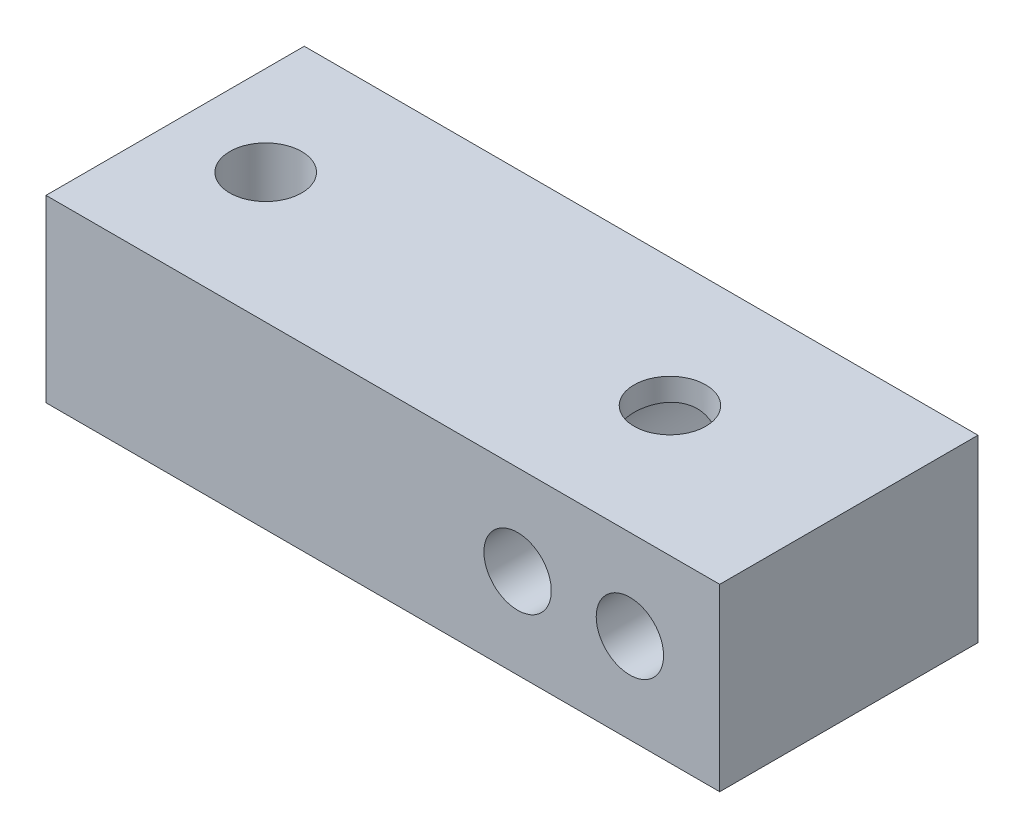
SolidWorks part; units mm, degrees
ref_plane "Front Plane" through (0, 0, 0) normal (0, 0, 1) x (1, 0, 0)
ref_plane "Top Plane" through (0, 0, 0) normal (0, 1, 0) x (1, 0, 0)
ref_plane "Right Plane" through (0, 0, 0) normal (1, 0, 0) x (0, 0, -1)
sketch "Sketch1" plane through (0, 0, 0) normal (0, 1, 0) x (1, 0, 0)
  line L1 (0, 0) -> (30, 0)
  line L2 (0, 0) -> (0, 11.5)
  line L3 (0, 11.5) -> (30, 11.5)
  line L4 (30, 0) -> (30, 11.5)
  dimension "D1" = 30
  dimension "D2" = 11.5
extrude "Boss-Extrude1" add sketch "Sketch1" along normal blind 8
sketch "Sketch2" plane through (0, 0, -11.5) normal (0, 0, -1) x (-1, 0, 0)
  circle A0 centre (-21, 4) radius 1.5
  circle A1 centre (-26, 4) radius 1.5
extrude "Cut-Extrude1" cut sketch "Sketch2" against normal through all
sketch "Sketch3" plane through (0, 0, 0) normal (0, -1, 0) x (1, 0, 0)
  circle A0 centre (21.9986, -5.7844) radius 1.5982
  circle A1 centre (4.0005, -5.7827) radius 1.601
extrude "Cut-Extrude2" cut sketch "Sketch3" against normal blind 10
sketch "Sketch4" plane through (0, 0, -11.5) normal (0, 0, -1) x (-1, 0, 0)
  arc A0 (-23.5, 5.6583) -> (-23.5, 2.3417) centre (-26, 4) ccw
  arc A1 (-23.5, 2.3417) -> (-23.5, 5.6583) centre (-21, 4) ccw
  dimension "D1" = 6
  dimension "D2" = 6
extrude "Cut-Extrude3" cut sketch "Sketch4" against normal blind 9
